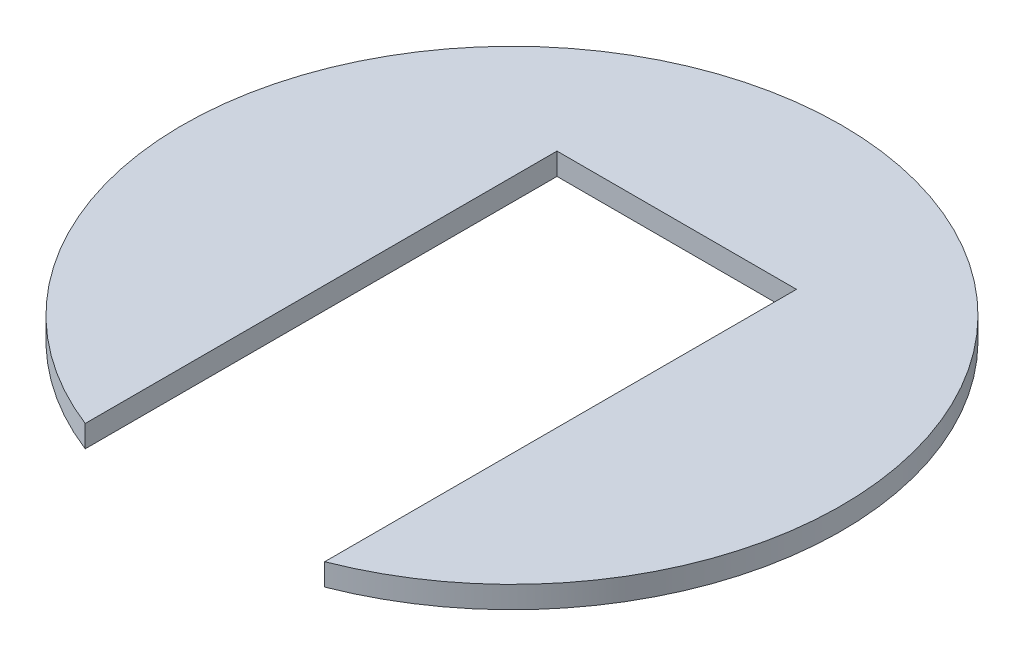
SolidWorks part; units mm, degrees
ref_plane "Front" through (0, 0, 0) normal (0, 0, 1) x (1, 0, 0)
ref_plane "Top" through (0, 0, 0) normal (0, 1, 0) x (1, 0, 0)
ref_plane "Right" through (0, 0, 0) normal (1, 0, 0) x (0, 0, -1)
sketch "Sketch1" plane through (0, 0, 0) normal (0, 1, 0) x (1, 0, 0)
  line L0 (0, 0) -> (0, 100.7374) construction
  line L2 (-54.5, -139.7489) -> (-54.5, 75)
  line L3 (-54.5, 75) -> (54.5, 75)
  line L4 (54.5, -139.7489) -> (54.5, 75)
  line L5 (0, 0) -> (43.1132, 0) construction
  arc A0 (54.5, -139.7489) -> (-54.5, -139.7489) centre (0, 0) ccw
  point P7 (0, 75)
  dimension "D1" = 300
  dimension "D2" = 109
  dimension "D3" = 75
extrude "Extrude1" add sketch "Sketch1" along normal blind 10
